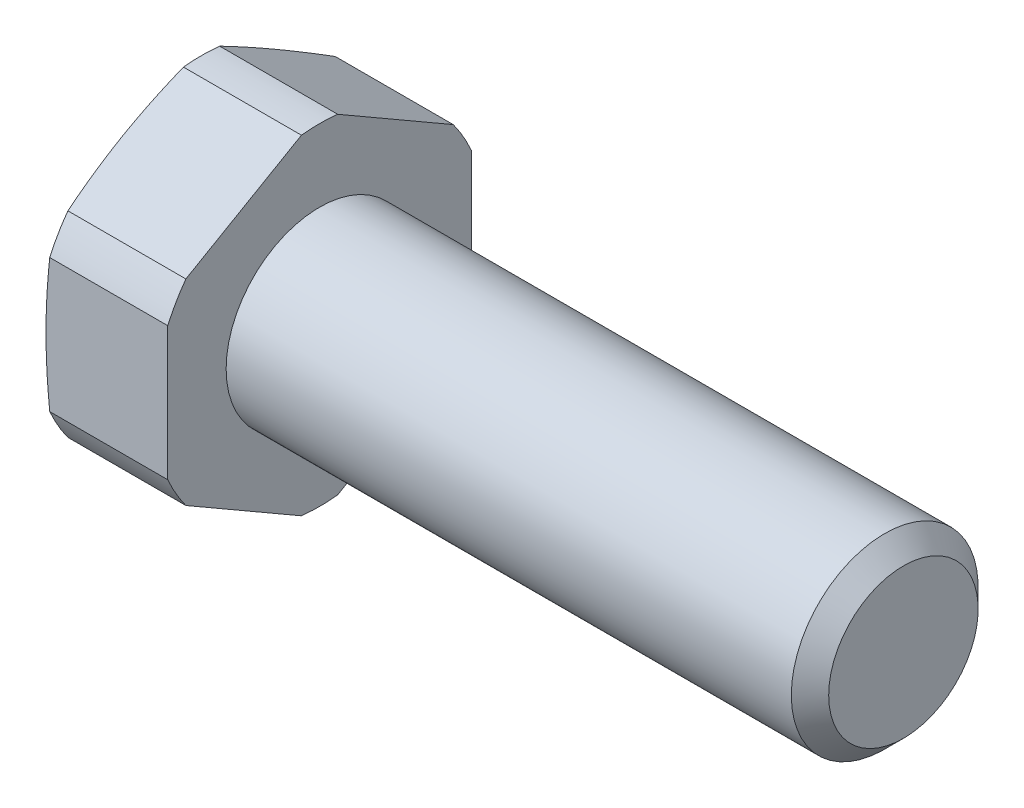
SolidWorks part; units mm, degrees
material "AISI 1020"
ref_plane "Спереди" through (0, 0, 0) normal (0, 0, 1) x (1, 0, 0)
ref_plane "Сверху" through (0, 0, 0) normal (0, 1, 0) x (1, 0, 0)
ref_plane "Справа" through (0, 0, 0) normal (1, 0, 0) x (0, 0, -1)
sketch "Эскиз1" plane through (0, 0, 0) normal (0, 0, 1) x (1, 0, 0)
  line L0 (-1000, 0) -> (49000, 0) construction
  line L1 (-5.3, 0) -> (-5.3, 6.175)
  line L2 (-5.3, 6.175) -> (-5.0521, 7.1)
  line L3 (-5.0521, 7.1) -> (0, 7.1)
  line L4 (0, 7.1) -> (0, 4)
  line L5 (0, 4) -> (24.2, 4)
  line L6 (25, 3.2) -> (25, 0)
  line L7 (25, 4) -> (25.625, 5.0825) construction
  line L8 (25.625, 5.0825) -> (26.25, 4) construction
  line L9 (26.25, 4) -> (25, 4) construction
  line L10 (25.625, 5.0825) -> (25.625, 4) construction
  line L11 (25.625, 5.0825) -> (0.625, 5.0825) construction
  line L12 (24.2, 4) -> (25, 3.2)
  line L13 (25, 4) -> (24.6, 3.6) construction
  line L14 (-5.3, 6.175) -> (-18.3, 6.175) construction
  line L15 (-5.3, 0) -> (25, 0)
  dimension "l_" = 25
  dimension "b_" = 25
  dimension "_d_" = 8
  dimension "D" = 12.35
  dimension "k_" = 5.3
  dimension "e_" = 14.2
  dimension "shag_" = 1.25
  dimension "dr" = 1.0825
  dimension "D1" = 0.8
  dimension "D2" = 15
  dimension "S_" = 13
revolve "Повернуть1" add sketch "Эскиз1" angle 360 about L0
cosmetic thread "Условное изображение резьбы1" parameters "D1"=25, "D2"=5.8349
sketch "Эскиз2" plane through (-5.3, 0, 0) normal (-1, 0, 0) x (0, 0, 1)
  line L1 (0, 7.5056) -> (-6.5, 3.7528)
  line L2 (-6.5, 3.7528) -> (-6.5, -3.7528)
  line L3 (-6.5, -3.7528) -> (0, -7.5056)
  line L4 (0, -7.5056) -> (6.5, -3.7528)
  line L5 (6.5, -3.7528) -> (6.5, 3.7528)
  line L6 (6.5, 3.7528) -> (0, 7.5056)
  circle A0 centre (0, 0) radius 6.5 construction
  dimension "D1" = 13
extrude "Вырез-Вытянуть1" cut sketch "Эскиз2" against normal up to surface (30.3 mm away) flip side to cut up to face at (25, 0, 3.2)
equation "\"D1@Эскиз1\"=\"_d_@Эскиз1\"/10"
equation "\"D@Эскиз1\"=\"S_@Эскиз1\"*0.95"
equation "\"D1@Эскиз2\"=\"S_@Эскиз1\""
equation "\"D1@Условное изображение резьбы1\"=\"b_@Эскиз1\""
equation "\"D2@Условное изображение резьбы1\"=\"_d_@Эскиз1\"-\"dr@Эскиз1\"*2"
